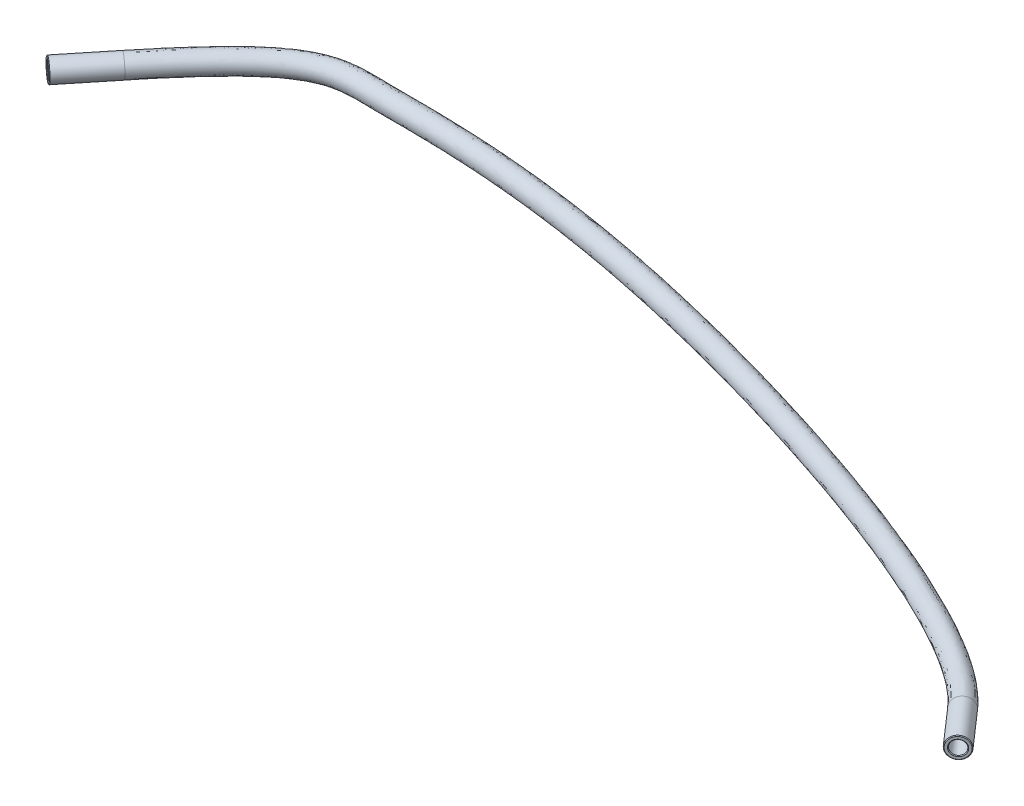
SolidWorks part; units mm, degrees
ref_plane "Front Plane" through (0, 0, 0) normal (0, 0, 1) x (1, 0, 0)
ref_plane "Top Plane" through (0, 0, 0) normal (0, 1, 0) x (1, 0, 0)
ref_plane "Right Plane" through (0, 0, 0) normal (1, 0, 0) x (0, 0, -1)
sketch3d "3DSketch1"
  line L0 (-109.9126, -99.5875, -21.9249) -> (-116.3264, -99.5875, -13.9938)
  line L1 (80.6644, -99.6875, 10.8405) -> (74.6041, -99.6875, 3.9186)
  spline S0 degree 3 poles (74.6041, -99.6875, 3.9186) (62.805, -99.6875, -9.5581) (-32.99, -99.6522, -42.8291) (-83.3254, -99.6022, -40.2685) (-93.6626, -99.5875, -42.019) (-109.9126, -99.5875, -21.9249) knots 0 0 0 0 0.304238 0.705959 1 1 1 1
sketch "Sketch1" plane through (35.6979, 0, 40.7731) normal (-0.6587, 0, -0.7524) x (-0.7524, 0, 0.6587)
  circle A0 centre (-53.5494, -99.6875) radius 2
  circle A1 centre (-53.5494, -99.6875) radius 1.3
  circle A2 centre (-53.5494, -99.6875) radius 3.5524 construction
  dimension "D1" = 2.6
  dimension "D2" = 4
sweep "Sweep1" add profiles "Sketch1" path "3DSketch1"
chamfer "Chamfer1" distance 0.127 angle 45 4 edges at (-114.7713, -99.5893, -12.7362) (-115.3156, -99.5887, -13.1764) (79.1597, -99.6875, 12.158) (79.6863, -99.6875, 11.6968)
